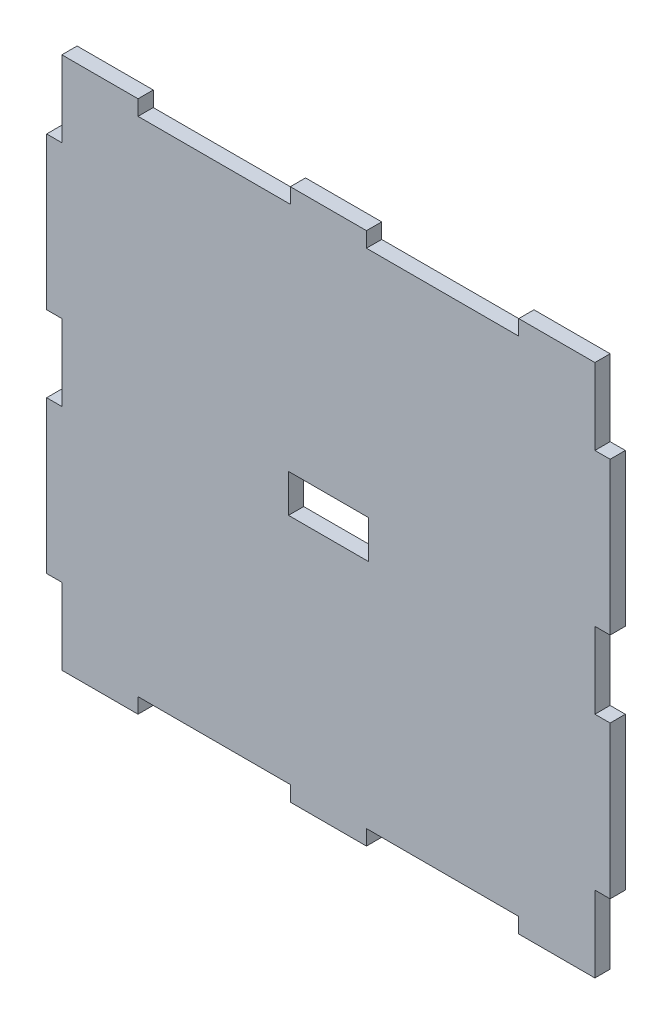
SolidWorks part; units mm, degrees
ref_plane "Front Plane" through (0, 0, 0) normal (0, 0, 1) x (1, 0, 0)
ref_plane "Top Plane" through (0, 0, 0) normal (0, 1, 0) x (1, 0, 0)
ref_plane "Right Plane" through (0, 0, 0) normal (1, 0, 0) x (0, 0, -1)
sketch "Sketch1" plane through (0, 0, 0) normal (0, 0, 1) x (1, 0, 0)
  line L1 (-35, -35) -> (35, -35)
  line L2 (-35, -35) -> (-35, 35)
  line L3 (-35, 35) -> (35, 35)
  line L4 (35, -35) -> (35, 35)
  line L5 (0, 35) -> (0, -35) construction
  line L6 (-35, 0) -> (35, 0) construction
  line L11 (0, 18) -> (0, -18) construction
  line L12 (-17.25, 0) -> (17.25, 0) construction
  point P0 (0, 0)
  point P4 (0, 0)
  dimension "D1" = 70
  dimension "D2" = 70
extrude "Boss-Extrude1" add sketch "Sketch1" against normal blind 2
sketch "Sketch2" plane through (0, 0, 0) normal (0, 0, 1) x (1, 0, 0)
  line L0 (-35, 35) -> (-25, 35)
  line L1 (35, 35) -> (-35, 35) construction
  line L2 (-25, 35) -> (-5, 35)
  line L3 (-5, 35) -> (5, 35)
  line L4 (5, 35) -> (25, 35)
  line L6 (35, 35) -> (35, 25)
  line L7 (-25, 33) -> (-5, 33)
  line L8 (-25, 33) -> (-25, 37)
  line L9 (-25, 37) -> (-5, 37)
  line L10 (-5, 33) -> (-5, 37)
  line L11 (-15, 37) -> (-15, 33) construction
  line L12 (-25, 35) -> (-5, 35) construction
  line L13 (5, 33) -> (25, 33)
  line L14 (5, 33) -> (5, 37)
  line L15 (5, 37) -> (25, 37)
  line L16 (25, 33) -> (25, 37)
  line L17 (15, 37) -> (15, 33) construction
  line L18 (5, 35) -> (25, 35) construction
  line L19 (35, -35) -> (35, 35) construction
  line L20 (35, 25) -> (35, 5)
  line L21 (35, 5) -> (35, -5)
  line L22 (35, -5) -> (35, -25)
  line L23 (-35, -35) -> (-25, -35)
  line L24 (35, -5) -> (33, -5)
  line L25 (35, -5) -> (35, -25)
  line L26 (35, -25) -> (33, -25)
  line L27 (33, -5) -> (33, -25)
  line L28 (35, 25) -> (33, 25)
  line L29 (35, 25) -> (35, 5)
  line L30 (35, 5) -> (33, 5)
  line L31 (33, 25) -> (33, 5)
  line L32 (-35, -35) -> (35, -35) construction
  line L33 (-25, -35) -> (-5, -35)
  line L34 (-5, -35) -> (5, -35)
  line L35 (5, -35) -> (25, -35)
  line L36 (-35, 35) -> (-35, 25)
  line L37 (-25, -35) -> (-5, -35)
  line L38 (-25, -35) -> (-25, -33)
  line L39 (-25, -33) -> (-5, -33)
  line L40 (-5, -35) -> (-5, -33)
  line L41 (5, -35) -> (25, -35)
  line L42 (5, -35) -> (5, -33)
  line L43 (5, -33) -> (25, -33)
  line L44 (25, -35) -> (25, -33)
  line L45 (-35, 35) -> (-35, -35) construction
  line L46 (-35, 25) -> (-35, 5)
  line L47 (-35, 5) -> (-35, -5)
  line L48 (-35, -5) -> (-35, -25)
  line L49 (-35, 25) -> (-37, 25)
  line L50 (-35, 25) -> (-33, 25)
  line L51 (-35, 25) -> (-35, 5)
  line L52 (-35, 5) -> (-33, 5)
  line L53 (-33, 25) -> (-33, 5)
  line L54 (-35, -5) -> (-33, -5)
  line L55 (-35, -5) -> (-35, -25)
  line L56 (-35, -25) -> (-33, -25)
  line L57 (-33, -5) -> (-33, -25)
  line L58 (-35, 25) -> (-35, 5)
  line L59 (-35, 5) -> (-37, 5)
  line L60 (-37, 25) -> (-37, 5)
  line L61 (-35, -5) -> (-37, -5)
  line L62 (-35, -5) -> (-35, -25)
  line L63 (-35, -25) -> (-37, -25)
  line L64 (-37, -5) -> (-37, -25)
  line L65 (-25, -35) -> (-5, -35)
  line L66 (-25, -35) -> (-25, -37)
  line L67 (-25, -37) -> (-5, -37)
  line L68 (-5, -35) -> (-5, -37)
  line L69 (5, -35) -> (25, -35)
  line L70 (5, -35) -> (5, -37)
  line L71 (5, -37) -> (25, -37)
  line L72 (25, -35) -> (25, -37)
  line L73 (35, -25) -> (37, -25)
  line L74 (35, -25) -> (35, -5)
  line L75 (35, -5) -> (37, -5)
  line L76 (37, -25) -> (37, -5)
  line L77 (35, 5) -> (37, 5)
  line L78 (35, 5) -> (35, 25)
  line L79 (35, 25) -> (37, 25)
  line L80 (37, 5) -> (37, 25)
  point P7 (15, 35)
  point P9 (-15, 35)
  point P10 (-15, 35)
  point P14 (15, 35)
  line M25 (35, -35) -> (35, 35)
  line M27 (-35, 35) -> (-35, -35)
  dimension "D1" = 10
  dimension "D2" = 20
  dimension "D3" = 10
  dimension "D4" = 20
  dimension "D5" = 4
  dimension "D6" = 20
  dimension "D7" = 20
  dimension "D8" = 4
  dimension "D9" = 10
  dimension "D10" = 20
  dimension "D11" = 10
  dimension "D12" = 20
  dimension "D13" = 2
  dimension "D14" = 2
  dimension "D15" = 10
  dimension "D16" = 20
  dimension "D17" = 10
  dimension "D18" = 20
  dimension "D19" = 20
  dimension "D20" = 20
  dimension "D21" = 2
  dimension "D22" = 2
  dimension "D23" = 10
  dimension "D24" = 20
  dimension "D25" = 10
  dimension "D26" = 20
  dimension "D27" = 2
  dimension "D28" = 2
  dimension "D29" = 2
  dimension "D30" = 2
  dimension "D31" = 2
  dimension "D32" = 2
  dimension "D33" = 2
  dimension "D34" = 2
sketch "Sketch3" plane through (0, 0, 0) normal (0, 0, 1) x (1, 0, 0)
  line L0 (-35, 35) -> (-25, 35)
  line L2 (-25, 35) -> (-5, 35)
  line L3 (-5, 35) -> (5, 35)
  line L4 (5, 35) -> (25, 35)
  line L6 (35, 35) -> (35, 25)
  line L7 (-25, 33) -> (-5, 33)
  line L8 (-25, 33) -> (-25, 37)
  line L9 (-25, 37) -> (-5, 37)
  line L10 (-5, 33) -> (-5, 37)
  line L11 (-15, 37) -> (-15, 33) construction
  line L12 (-25, 35) -> (-5, 35) construction
  line L13 (5, 33) -> (25, 33)
  line L14 (5, 33) -> (5, 37)
  line L15 (5, 37) -> (25, 37)
  line L16 (25, 33) -> (25, 37)
  line L17 (15, 37) -> (15, 33) construction
  line L18 (5, 35) -> (25, 35) construction
  line L20 (35, 25) -> (35, 5)
  line L21 (35, 5) -> (35, -5)
  line L22 (35, -5) -> (35, -25)
  line L23 (-35, -35) -> (-25, -35)
  line L24 (35, -5) -> (33, -5)
  line L25 (35, -5) -> (35, -25)
  line L26 (35, -25) -> (33, -25)
  line L27 (33, -5) -> (33, -25)
  line L28 (35, 25) -> (33, 25)
  line L29 (35, 25) -> (35, 5)
  line L30 (35, 5) -> (33, 5)
  line L31 (33, 25) -> (33, 5)
  line L33 (-25, -35) -> (-5, -35)
  line L34 (-5, -35) -> (5, -35)
  line L35 (5, -35) -> (25, -35)
  line L36 (-35, 35) -> (-35, 25)
  line L37 (-25, -35) -> (-5, -35)
  line L38 (-25, -35) -> (-25, -33)
  line L39 (-25, -33) -> (-5, -33)
  line L40 (-5, -35) -> (-5, -33)
  line L41 (5, -35) -> (25, -35)
  line L42 (5, -35) -> (5, -33)
  line L43 (5, -33) -> (25, -33)
  line L44 (25, -35) -> (25, -33)
  line L46 (-35, 25) -> (-35, 5)
  line L47 (-35, 5) -> (-35, -5)
  line L48 (-35, -5) -> (-35, -25)
  line L49 (-35, 25) -> (-37, 25)
  line L50 (-35, 25) -> (-33, 25)
  line L51 (-35, 25) -> (-35, 5)
  line L52 (-35, 5) -> (-33, 5)
  line L53 (-33, 25) -> (-33, 5)
  line L54 (-35, -5) -> (-33, -5)
  line L55 (-35, -5) -> (-35, -25)
  line L56 (-35, -25) -> (-33, -25)
  line L57 (-33, -5) -> (-33, -25)
  line L58 (-35, 25) -> (-35, 5)
  line L59 (-35, 5) -> (-37, 5)
  line L60 (-37, 25) -> (-37, 5)
  line L61 (-35, -5) -> (-37, -5)
  line L62 (-35, -5) -> (-35, -25)
  line L63 (-35, -25) -> (-37, -25)
  line L64 (-37, -5) -> (-37, -25)
  line L65 (-25, -35) -> (-5, -35)
  line L66 (-25, -35) -> (-25, -37)
  line L67 (-25, -37) -> (-5, -37)
  line L68 (-5, -35) -> (-5, -37)
  line L69 (5, -35) -> (25, -35)
  line L70 (5, -35) -> (5, -37)
  line L71 (5, -37) -> (25, -37)
  line L72 (25, -35) -> (25, -37)
  line L73 (35, -25) -> (37, -25)
  line L74 (35, -25) -> (35, -5)
  line L75 (35, -5) -> (37, -5)
  line L76 (37, -25) -> (37, -5)
  line L77 (35, 5) -> (37, 5)
  line L78 (35, 5) -> (35, 25)
  line L79 (35, 25) -> (37, 25)
  line L80 (37, 5) -> (37, 25)
  point P7 (15, 35)
  point P9 (-15, 35)
  point P10 (-15, 35)
  point P14 (15, 35)
  dimension "D1" = 10
  dimension "D2" = 20
  dimension "D3" = 10
  dimension "D4" = 20
  dimension "D5" = 4
  dimension "D6" = 20
  dimension "D7" = 20
  dimension "D8" = 4
  dimension "D9" = 10
  dimension "D10" = 20
  dimension "D11" = 10
  dimension "D12" = 20
  dimension "D13" = 2
  dimension "D14" = 2
  dimension "D15" = 10
  dimension "D16" = 20
  dimension "D17" = 10
  dimension "D18" = 20
  dimension "D19" = 20
  dimension "D20" = 20
  dimension "D21" = 2
  dimension "D22" = 2
  dimension "D23" = 10
  dimension "D24" = 20
  dimension "D25" = 10
  dimension "D26" = 20
  dimension "D27" = 2
  dimension "D28" = 2
  dimension "D29" = 2
  dimension "D30" = 2
  dimension "D31" = 2
  dimension "D32" = 2
  dimension "D33" = 2
  dimension "D34" = 2
extrude "Boss-Extrude2" add sketch "Sketch2" against normal blind 2 contours L49 L60 L59 M27 | L61 L64 L63 M27 | L73 L76 L75 M25 | L77 L80 L79 M25
extrude "Cut-Extrude1" cut sketch "Sketch3" against normal blind 2 contours L7 L10 L2 L8 | L13 L16 L4 L14 | L33 L40 L39 L38 | L35 L44 L43 L42
sketch "Sketch4" plane through (0, 0, 0) normal (0, 0, 1) x (1, 0, 0)
  line L1 (-5.24, -2.5) -> (5.24, -2.5)
  line L2 (-5.24, -2.5) -> (-5.24, 2.5)
  line L3 (-5.24, 2.5) -> (5.24, 2.5)
  line L4 (5.24, -2.5) -> (5.24, 2.5)
  line L5 (0, 2.5) -> (0, -2.5) construction
  line L6 (-5.24, 0) -> (5.24, 0) construction
  point P0 (0, 0)
  dimension "D1" = 10.48
  dimension "D2" = 5
extrude "Cut-Extrude2" cut sketch "Sketch4" against normal blind 10
